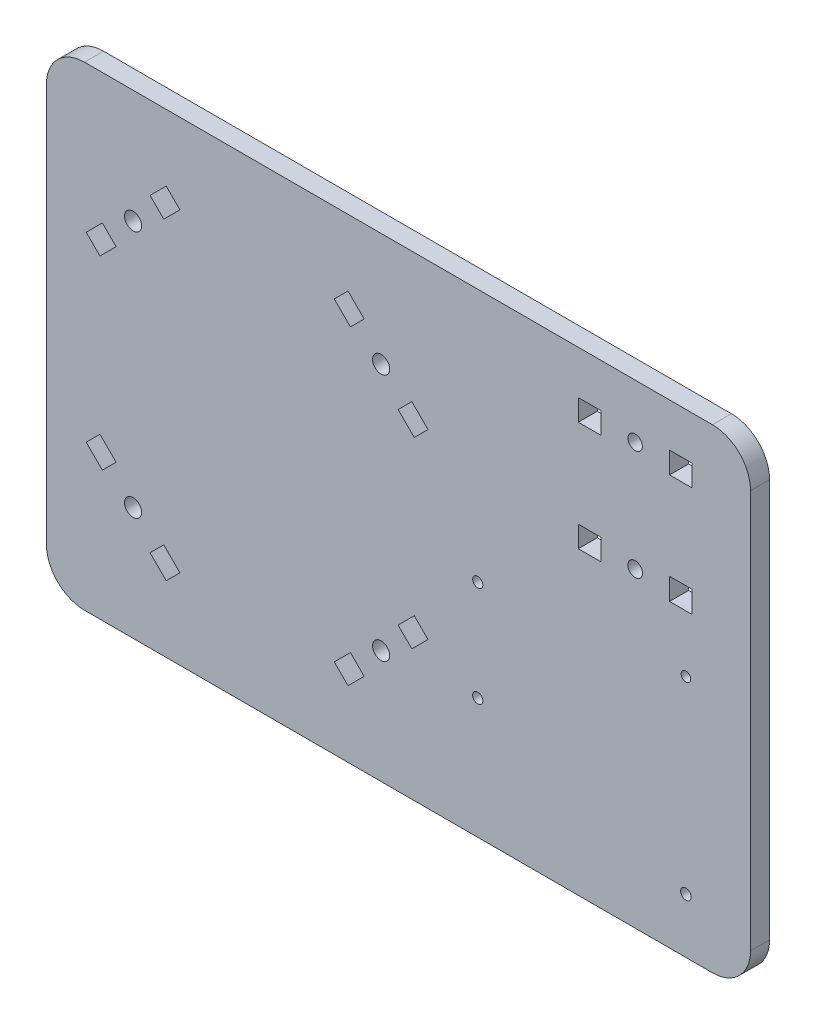
SolidWorks part; units mm, degrees
ref_plane "Front Plane" through (0, 0, 0) normal (0, 0, 1) x (1, 0, 0)
ref_plane "Top Plane" through (0, 0, 0) normal (0, 1, 0) x (1, 0, 0)
ref_plane "Right Plane" through (0, 0, 0) normal (1, 0, 0) x (0, 0, -1)
sketch "Sketch2" plane through (0, 0, 0) normal (0, 0, 1) x (1, 0, 0)
  line L29 (185, -142.6594) -> (185, -37.9314)
  line L31 (175, -27.9314) -> (10, -27.9314)
  line L33 (175, -152.6594) -> (10, -152.6594)
  line L34 (0, -37.9314) -> (0, -142.6594)
  line L50 (163.7283, -44.9924) -> (169.6553, -44.9924)
  line L51 (163.7283, -44.9924) -> (163.7283, -39.3468)
  line L52 (169.6553, -44.9924) -> (169.6553, -39.3468)
  line L53 (163.7283, -39.3468) -> (169.6553, -39.3468)
  line L54 (139.7403, -44.9924) -> (145.6673, -44.9924)
  line L55 (139.7403, -44.9924) -> (139.7403, -39.3781)
  line L56 (145.6673, -44.9924) -> (145.6673, -39.3781)
  line L57 (139.7403, -39.3781) -> (145.6673, -39.3781)
  line L58 (163.7283, -73.7784) -> (169.6553, -73.7784)
  line L59 (163.7283, -73.7784) -> (163.7283, -68.0524)
  line L60 (169.6553, -73.7784) -> (169.6553, -68.0524)
  line L61 (163.7283, -68.0524) -> (169.6553, -68.0524)
  line L62 (139.7403, -73.7784) -> (145.6673, -73.7784)
  line L63 (139.7403, -73.7784) -> (139.7403, -68.1856)
  line L64 (145.6673, -73.7784) -> (145.6673, -68.1856)
  line L65 (139.7403, -68.1856) -> (145.6673, -68.1856)
  line L66 (10.4463, -114.1815) -> (14.689, -118.4241)
  line L67 (10.4463, -114.1815) -> (14.0526, -110.5753)
  line L68 (14.689, -118.4241) -> (18.2952, -114.8179)
  line L69 (14.0526, -110.5753) -> (18.2952, -114.8179)
  line L111 (0, -90.2954) -> (108.5303, -90.2954) construction
  line L112 (22.7571, -122.886) -> (22.7571, -57.7048) construction
  line L113 (12.5677, -116.3028) -> (16.1739, -112.6966) construction
  line L114 (55.3477, -27.9314) -> (55.3477, -152.6594) construction
  line L115 (29.3402, -133.0754) -> (32.9465, -129.4691) construction
  line L116 (35.0678, -131.5905) -> (30.8252, -127.3478)
  line L117 (27.2189, -130.9541) -> (30.8252, -127.3478)
  line L118 (31.4616, -135.1967) -> (35.0678, -131.5905)
  line L119 (31.4616, -135.1967) -> (27.2189, -130.9541)
  line L120 (98.1277, -116.3028) -> (94.5214, -112.6966) construction
  line L121 (96.6427, -110.5753) -> (92.4001, -114.8179)
  line L122 (96.0064, -118.4241) -> (92.4001, -114.8179)
  line L123 (100.249, -114.1815) -> (96.6427, -110.5753)
  line L124 (100.249, -114.1815) -> (96.0064, -118.4241)
  line L125 (68.9964, -141.8278) -> (106.8801, -103.9442) construction
  line L126 (81.3551, -133.0754) -> (77.7489, -129.4691) construction
  line L127 (79.2338, -135.1967) -> (83.4764, -130.9541)
  line L128 (79.2338, -135.1967) -> (75.6275, -131.5905)
  line L129 (22.7571, -122.886) -> (88.906, -56.737) construction
  line L130 (83.4764, -130.9541) -> (79.8702, -127.3478)
  line L131 (41.6989, -141.8278) -> (3.8152, -103.9442) construction
  line L132 (0, 0) -> (0, -90.2954) construction
  line L133 (75.6275, -131.5905) -> (79.8702, -127.3478)
  line L134 (41.6989, -38.763) -> (3.8152, -76.6466) construction
  line L135 (22.7571, -57.7048) -> (88.906, -123.8537) construction
  line L136 (81.3551, -47.5154) -> (77.7489, -51.1216) construction
  line L137 (68.9964, -38.763) -> (106.8801, -76.6466) construction
  line L138 (98.1277, -64.2879) -> (94.5214, -67.8942) construction
  line L139 (29.3402, -47.5154) -> (32.9465, -51.1216) construction
  line L140 (12.5677, -64.2879) -> (16.1739, -67.8942) construction
  line L141 (75.6275, -49.0003) -> (79.8702, -53.2429)
  line L142 (83.4764, -49.6367) -> (79.8702, -53.2429)
  line L143 (79.2338, -45.3941) -> (75.6275, -49.0003)
  line L144 (79.2338, -45.3941) -> (83.4764, -49.6367)
  line L145 (100.249, -66.4093) -> (96.0064, -62.1666)
  line L146 (100.249, -66.4093) -> (96.6427, -70.0155)
  line L147 (96.0064, -62.1666) -> (92.4001, -65.7729)
  line L148 (96.6427, -70.0155) -> (92.4001, -65.7729)
  line L149 (31.4616, -45.3941) -> (27.2189, -49.6367)
  line L150 (31.4616, -45.3941) -> (35.0678, -49.0003)
  line L151 (27.2189, -49.6367) -> (30.8252, -53.2429)
  line L152 (35.0678, -49.0003) -> (30.8252, -53.2429)
  line L153 (14.0526, -70.0155) -> (18.2952, -65.7729)
  line L154 (14.689, -62.1666) -> (18.2952, -65.7729)
  line L155 (10.4463, -66.4093) -> (14.0526, -70.0155)
  line L156 (10.4463, -66.4093) -> (14.689, -62.1666)
  arc A0 (185, -142.6594) -> (175, -152.6594) centre (175, -142.6594) cw
  arc A2 (10, -152.6594) -> (0, -142.6594) centre (10, -142.6594) cw
  arc A3 (10, -27.9314) -> (0, -37.9314) centre (10, -37.9314) ccw
  arc A4 (185, -37.9314) -> (175, -27.9314) centre (175, -37.9314) ccw
  circle A7 centre (154.6946, -42.0768) radius 1.8926
  circle A8 centre (154.6904, -70.942) radius 1.9315
  circle A9 centre (113.3305, -94.5869) radius 1.329
  circle A10 centre (168.0305, -88.7305) radius 1.2561
  circle A11 centre (22.7571, -122.886) radius 2.25
  circle A13 centre (113.3305, -120.9635) radius 1.3462
  circle A14 centre (168.0305, -138.2305) radius 1.3886
  circle A15 centre (87.9383, -122.886) radius 2.25
  circle A16 centre (87.9383, -57.7048) radius 2.25
  circle A17 centre (22.7571, -57.7048) radius 2.25
  circle A18 centre (168.0305, -88.7305) radius 1.5 construction
  circle A19 centre (168.0305, -138.2305) radius 1.5 construction
  circle A22 centre (113.3305, -120.9635) radius 1.5 construction
  circle A23 centre (113.3305, -94.5869) radius 1.5 construction
  point P1 (14.3708, -114.4997)
  point P2 (16.4921, -116.621)
  point P47 (55.3477, -90.2954)
  point P49 (22.7571, -90.2954)
  point P57 (185, -152.6594)
  point P63 (185, -153.7832)
  point P84 (0, 0)
  point P89 (0, 0)
  point P90 (0, 0)
  dimension "D2" = 10
  dimension "D3" = 22.7571
  dimension "D18" = 4.5
  dimension "D14" = 10
  dimension "D4" = 32.5906
  dimension "D5" = 27.9314
  dimension "D6" = 124.728
  dimension "D7" = 11.86
  dimension "D8" = 5.1
  dimension "D9" = 6
  dimension "D10" = 135
  dimension "D13" = 185
extrude "Boss-Extrude3" add sketch "Sketch2" along normal blind 5
